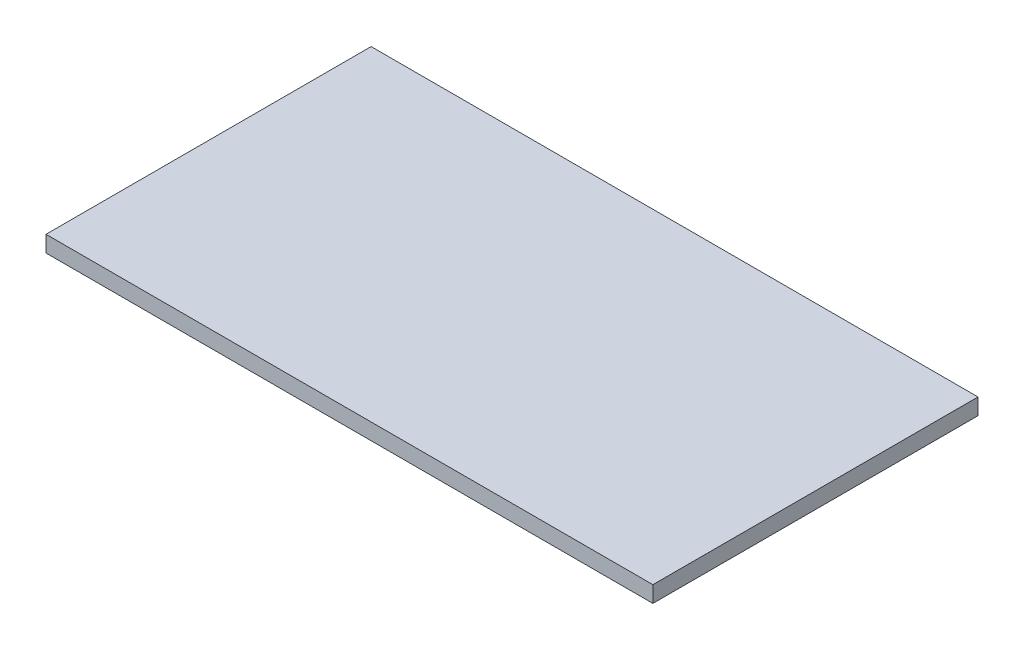
SolidWorks part; units mm, degrees
ref_plane "Ebene vorne" through (0, 0, 0) normal (0, 0, 1) x (1, 0, 0)
ref_plane "Ebene oben" through (0, 0, 0) normal (0, 1, 0) x (1, 0, 0)
ref_plane "Ebene rechts" through (0, 0, 0) normal (1, 0, 0) x (0, 0, -1)
sketch "Skizze1" plane through (0, 0, 0) normal (0, 1, 0) x (1, 0, 0)
  line L0 (-280, 0) -> (280, 0) construction
  line L1 (-280, -166) -> (280, -166)
  line L2 (-280, -166) -> (-280, 134)
  line L3 (-280, 134) -> (280, 134)
  line L4 (280, -166) -> (280, 134)
  dimension "D1" = 560
  dimension "D2" = 300
  dimension "D3" = 166
extrude "Aufsatz-Linear austragen1" add sketch "Skizze1" along normal blind 15
